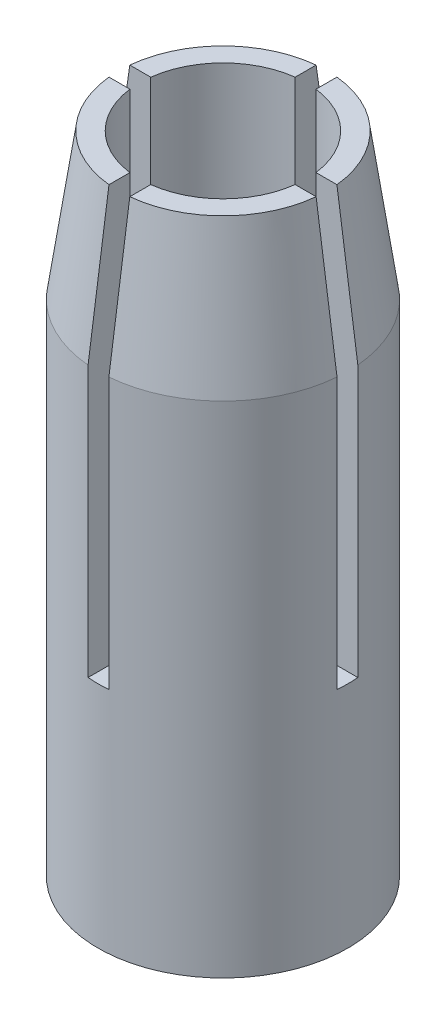
SolidWorks part; units mm, degrees
ref_plane "Спереди" through (0, 0, 0) normal (0, 0, 1) x (1, 0, 0)
ref_plane "Сверху" through (0, 0, 0) normal (0, 1, 0) x (1, 0, 0)
ref_plane "Справа" through (0, 0, 0) normal (1, 0, 0) x (0, 0, -1)
sketch "Эскиз1" plane through (0, 0, 0) normal (0, 0, 1) x (1, 0, 0)
  line L0 (0, 0) -> (0, 15.5) construction
  line L1 (0, 15.5) -> (2.5, 15.5)
  line L2 (2.5, 15.5) -> (3, 12)
  line L3 (3, 12) -> (3, 0)
  line L4 (3, 0) -> (0, 0)
  line L5 (0, 0) -> (0, 15.5)
  dimension "D1" = 15.5
  dimension "D2" = 6
  dimension "D3" = 3.5
  dimension "D4" = 5
revolve "Повернуть1" add sketch "Эскиз1" angle 360 about L0
sketch "Эскиз2" plane through (0, 15.5, 0) normal (0, 1, 0) x (1, 0, 0)
  line L0 (-0.25, 6.25) -> (0.25, 6.25)
  line L1 (-6.25, 0.25) -> (-6.25, -0.25) construction
  line L2 (-6.25, 0.25) -> (6.25, 0.25) construction
  line L3 (0.25, 6.25) -> (0.25, 0.25)
  line L4 (0.25, 0.25) -> (6.25, 0.25)
  line L5 (6.25, 0.25) -> (6.25, -0.25)
  line L6 (6.25, -0.25) -> (0.25, -0.25)
  line L7 (0.25, -0.25) -> (0.25, -6.25)
  line L8 (0.25, -6.25) -> (-0.25, -6.25)
  line L9 (-0.25, -6.25) -> (-0.25, -0.25)
  line L10 (-0.25, -0.25) -> (-6.25, -0.25)
  line L11 (-6.25, -0.25) -> (-6.25, 0.25)
  line L12 (-6.25, 0.25) -> (-0.25, 0.25)
  line L13 (-0.25, 0.25) -> (-0.25, 6.25)
  line L14 (-6.25, -0.25) -> (6.25, -0.25) construction
  line L15 (6.25, 0.25) -> (6.25, -0.25) construction
  line L16 (0, 0.25) -> (0, -0.25) construction
  line L17 (-6.25, 0) -> (6.25, 0) construction
  line L18 (0, 2.5) -> (0, -2.5) construction
  line L19 (-2.5, 0) -> (2.5, 0) construction
  line L20 (0, 6.25) -> (0, -6.25) construction
  line L21 (6.25, 0) -> (-6.25, 0) construction
  circle A0 centre (0, 0) radius 2.5 construction
  dimension "D1" = 0.5
  dimension "D2" = 6
extrude "Вырез-Вытянуть1" cut sketch "Эскиз2" against normal blind 10
sketch "Эскиз3" plane through (0, 0, 0) normal (0, -1, 0) x (1, 0, 0)
  circle A0 centre (0, 0) radius 2
  dimension "D1" = 4
extrude "Вырез-Вытянуть2" cut sketch "Эскиз3" against normal through all
